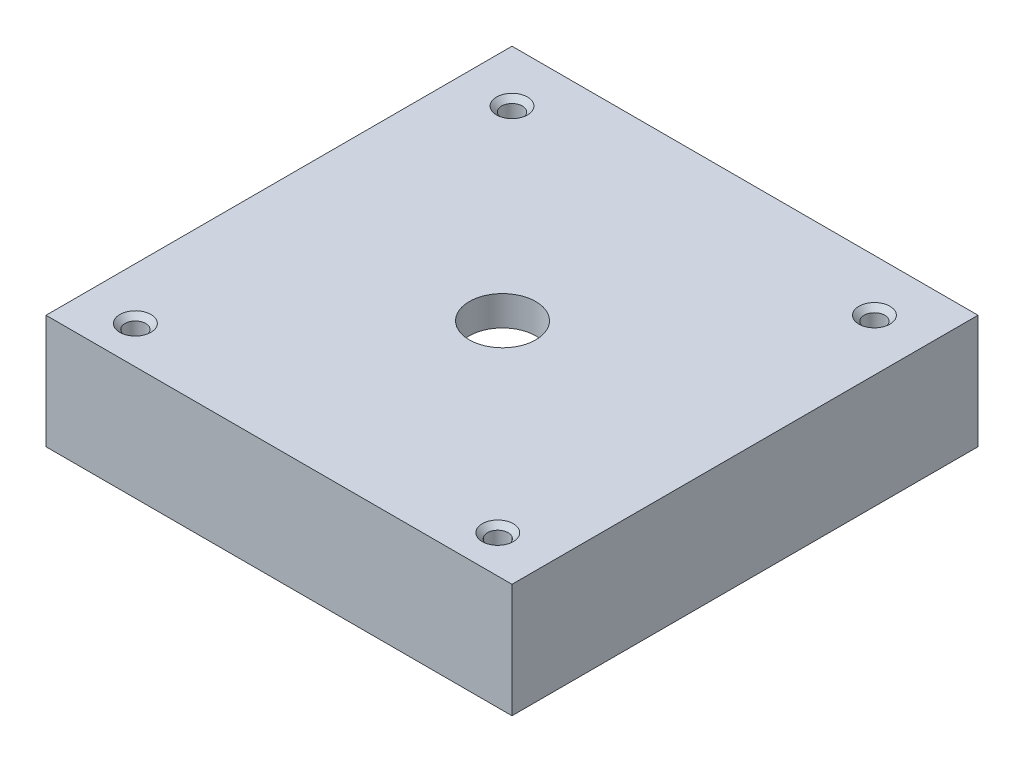
SolidWorks part; units mm, degrees
ref_plane "Front" through (0, 0, 0) normal (0, 0, 1) x (1, 0, 0)
ref_plane "Top" through (0, 0, 0) normal (0, 1, 0) x (1, 0, 0)
ref_plane "Right" through (0, 0, 0) normal (1, 0, 0) x (0, 0, -1)
sketch "Sketch1" plane through (0, 0, 0) normal (0, 1, 0) x (1, 0, 0)
  line L1 (0, 0) -> (90, 0)
  line L2 (0, 0) -> (0, 90.01)
  line L3 (0, 90.01) -> (90, 90.01)
  line L4 (90, 0) -> (90, 90.01)
  dimension "D1" = 90.01
  dimension "D2" = 90
extrude "Boss-Extrude1" add sketch "Sketch1" along normal blind 22
sketch "Sketch2" plane through (0, 0, 0) normal (0, -1, 0) x (1, 0, 0)
  line L0 (0, -45.005) -> (90, -45.005) construction
  line L1 (0, -90.01) -> (0, 0) construction
  line L2 (90, 0) -> (90, -90.01) construction
  line L3 (90, -45.005) -> (45, 0) construction
  line L4 (0, 0) -> (90, 0) construction
  line L5 (45, 0) -> (45, -90.01) construction
  line L6 (90, -90.01) -> (0, -90.01) construction
  line L8 (79.997, -7.2656) -> (9.997, -7.2656) construction
  circle A0 centre (9.997, -7.2656) radius 2
  circle A1 centre (9.997, -80.01) radius 2
  circle A2 centre (79.997, -7.2656) radius 2
  circle A3 centre (79.997, -80.01) radius 2
  dimension "D3" = 4
extrude "Cut-Extrude1" cut sketch "Sketch2" against normal through all and the other way through all
sketch "Sketch3" plane through (0, 0, 0) normal (0, -1, 0) x (1, 0, 0)
  line L0 (26.0928, -32.2642) -> (63.8998, -32.2642) construction
  line L1 (26.0928, -32.2642) -> (44.9963, -65.006) construction
  line L2 (80.4182, -43.54) -> (62.3324, -74.9789) construction
  line L3 (8.7723, -42.2642) -> (27.6758, -75.006) construction
  line L4 (26.0928, -12.2642) -> (63.8998, -12.2642) construction
  line L5 (44.9963, -43.1781) -> (44.9963, -20.8223) construction
  line L6 (44.9963, -43.1781) -> (23.7578, -53.5368) construction
  line L7 (63.8998, -32.2642) -> (44.9963, -65.006) construction
  line L8 (44.9963, -43.1781) -> (64.6766, -54.5405) construction
  line L9 (45, 0) -> (45, -90.01) construction
  line L10 (0, 0) -> (90, 0) construction
  line L11 (0, -90.01) -> (90, -90.01) construction
  line L12 (0, -45.005) -> (90, -45.005) construction
  line L13 (0, 0) -> (0, -90.01) construction
  line L14 (90, 0) -> (90, -90.01) construction
  line L15 (26.0928, -11.7642) -> (63.8998, -11.7642)
  line L16 (8.3393, -42.5142) -> (27.2428, -75.256)
  line L17 (80.8421, -43.8059) -> (62.7658, -75.2282)
  circle A0 centre (44.9963, -43.1781) radius 21.8279 construction
  circle A1 centre (26.0928, -32.2642) radius 2 construction
  circle A2 centre (63.8998, -32.2642) radius 2 construction
  circle A3 centre (44.9963, -65.006) radius 2 construction
  arc A4 (26.0928, -12.2642) -> (8.7723, -42.2642) centre (26.0928, -32.2642) ccw construction
  circle A5 centre (23.7578, -53.5368) radius 1.4 construction
  arc A6 (27.6758, -75.006) -> (62.3324, -74.9789) centre (44.9963, -65.006) ccw construction
  circle A7 centre (64.6766, -54.5405) radius 1.4 construction
  circle A8 centre (44.9963, -20.8223) radius 1.4 construction
  arc A9 (80.4182, -43.54) -> (63.8998, -12.2642) centre (63.8998, -32.2642) ccw construction
  arc A10 (80.8421, -43.8059) -> (63.8998, -11.7642) centre (63.8998, -32.2642) ccw
  arc A11 (26.0928, -11.7642) -> (8.3393, -42.5142) centre (26.0928, -32.2642) ccw
  arc A12 (27.2428, -75.256) -> (62.7658, -75.2282) centre (44.9963, -65.006) ccw
  dimension "D3" = 4
  dimension "D4" = 4
  dimension "D5" = 4
  dimension "D6" = 40
  dimension "D7" = 40
  dimension "D9" = 2.8
  dimension "D10" = 2.8
  dimension "D11" = 2.8
  dimension "D1" = 37.807
  dimension "D2" = 37.807
  dimension "D8" = 37.807
  dimension "D12" = 116
  dimension "D13" = 124
  dimension "D14" = 23.63
  dimension "D15" = 22.3558
  dimension "D16" = 22.7248
  dimension "D17" = 0.5
extrude "Cut-Extrude2" cut sketch "Sketch3" against normal blind 16.25
sketch "Sketch4" plane through (0, 16.25, 0) normal (0, -1, 0) x (1, 0, 0)
  line L0 (0, -45.005) -> (90, -45.005) construction
  line L1 (0, 0) -> (0, -90.01) construction
  line L2 (90, 0) -> (90, -90.01) construction
  line L3 (90, -45.005) -> (45, 0) construction
  line L4 (0, 0) -> (90, 0) construction
  line L5 (45, 0) -> (45, -90.01) construction
  line L6 (0, -90.01) -> (90, -90.01) construction
  circle A0 centre (44.9963, -43.1781) radius 6.4169
extrude "Cut-Extrude3" cut sketch "Sketch4" against normal through all
chamfer "Chamfer1" distance 1 angle 45 4 edges at (9.997, 22, -78.01) (9.997, 22, -9.2656) (79.997, 22, -78.01) (79.997, 22, -9.2656)
equation "\"d_racor\"= 11.8"
equation "\"h_alphasense\"= 5"
equation "\"h_chamber\"= 13"
equation "\"d_alphasense\" = 32.4mm"
equation "\"d_chamber\"= 19"
equation "\"h_base\"= 25 - \"h_chamber\" - \"h_alphasense\"-1"
equation "\"d_thread\"= 2.5"
equation "\"length_thread\"=10"
equation "\"D3@Sketch2\"= \"clip_thread_hole\""
equation "\"length_racor\"= 10"
equation "\"d_pipe\"=8"
equation "\"clip_thread_hole\" = 4"
equation "\"clip_thread_tap_drill\" = 3.5"
